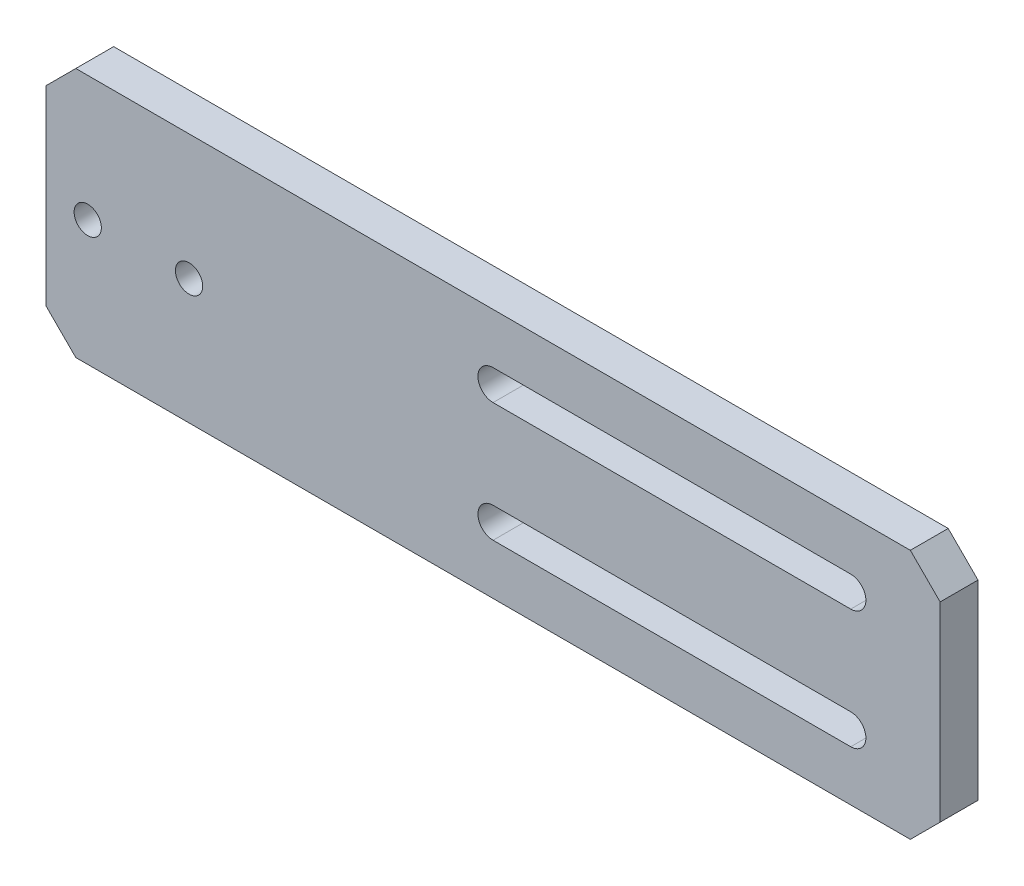
SolidWorks part; units mm, degrees
ref_plane "Front Plane" through (0, 0, 0) normal (0, 0, 1) x (1, 0, 0)
ref_plane "Top Plane" through (0, 0, 0) normal (0, 1, 0) x (1, 0, 0)
ref_plane "Right Plane" through (0, 0, 0) normal (1, 0, 0) x (0, 0, -1)
sketch "Sketch1" plane through (0, 0, 0) normal (0, 0, 1) x (1, 0, 0)
  line L1 (-100, 21) -> (100, 21)
  line L2 (-100, 21) -> (-100, -21)
  line L3 (-100, -21) -> (100, -21)
  line L4 (100, 21) -> (100, -21)
  line L5 (-100, 21) -> (100, -21) construction
  line L6 (-100, -21) -> (100, 21) construction
  point P0 (0, 0)
  dimension "D1" = 200
  dimension "D2" = 42
extrude "Boss-Extrude1" add sketch "Sketch1" along normal blind 6.35
sketch "Sketch3" plane through (0, 0, 6.35) normal (0, 0, 1) x (1, 0, 0)
  line L0 (-60, 10) -> (-60, -10) construction
  line L1 (-100, 21) -> (-100, -21) construction
  circle A0 centre (-60, 10) radius 2
  circle A1 centre (-60, -10) radius 2
  point P4 (-60, 0)
  dimension "D1" = 4
  dimension "D2" = 20
  dimension "D3" = 40
sketch "Sketch4" plane through (0, 0, 6.35) normal (0, 0, 1) x (1, 0, 0)
  line L0 (-100, 21) -> (-100, -21) construction
  line L1 (100, -21) -> (100, 21) construction
  circle A0 centre (-76, 0) radius 2.286
  circle A1 centre (80, 0) radius 2.286 construction
  dimension "D2" = 4.572
  dimension "D3" = 20
  dimension "D1" = 24
  dimension "D4" = 156
extrude "Cut-Extrude3" cut sketch "Sketch4" against normal through all
chamfer "Chamfer1" distance 5 angle 45 4 edges at (-100, 21, 3.175) (-100, -21, 3.175) (100, 21, 3.175) (100, -21, 3.175)
sketch "Sketch5" [suppressed] plane through (0, 0, 6.35) normal (0, 0, 1) x (1, 0, 0)
  line L0 (100, -16) -> (100, 16) construction
  circle A0 centre (77, 0) radius 11
  dimension "D1" = 22
  dimension "D2" = 23
extrude "Cut-Extrude4" [suppressed] cut sketch "Sketch5" against normal blind 25
sketch "Sketch8" plane through (0, 0, 6.35) normal (0, 0, 1) x (1, 0, 0)
  line L4 (25.5, 3.175) -> (10.5, 3.175)
  line L5 (10.5, 3.175) -> (10.5, -3.175)
  line L6 (10.5, -3.175) -> (25.5, -3.175)
  line L7 (25.5, -3.175) -> (25.5, 3.175)
  line L8 (25.5, 3.175) -> (10.5, 3.175)
  line L9 (10.5, 3.175) -> (10.5, -3.175)
  line L10 (10.5, -3.175) -> (25.5, -3.175)
  line L11 (25.5, -3.175) -> (25.5, 3.175)
  dimension "D1" = 0
extrude "Cut-Extrude7" [suppressed] cut sketch "Sketch8" against normal through all
sketch "Sketch9" plane through (0, 0, 6.35) normal (0, 0, 1) x (1, 0, 0)
  circle A0 centre (80, 0) radius 2.286 construction
  circle A1 centre (80, 0) radius 2.286
extrude "Cut-Extrude8" cut sketch "Sketch9" against normal through all
sketch "Sketch10" [suppressed] plane through (0, 0, 6.35) normal (0, 0, 1) x (1, 0, 0)
  circle A0 centre (80, 0) radius 15
  dimension "D1" = 25
extrude "Cut-Extrude9" [suppressed] cut sketch "Sketch10" against normal through all
sketch "Sketch11" plane through (0, 0, 6.35) normal (0, 0, 1) x (1, 0, 0)
  circle A0 centre (95.5563, 15.5563) radius 1.5 construction
  circle A1 centre (64.4437, 15.5563) radius 1.5 construction
  circle A2 centre (95.5563, -15.5563) radius 1.5 construction
  circle A3 centre (64.4437, -15.5563) radius 1.5 construction
  circle A4 centre (95.5563, 15.5563) radius 1.5
  circle A5 centre (64.4437, 15.5563) radius 1.5
  circle A6 centre (95.5563, -15.5563) radius 1.5
  circle A7 centre (64.4437, -15.5563) radius 1.5
sketch "Sketch12" plane through (0, 0, 6.35) normal (0, 0, 1) x (1, 0, 0)
  line L0 (-100, 16) -> (-100, -16) construction
  circle A0 centre (-93, 0) radius 2.286
  point P4 (-100, 0)
  dimension "D1" = 4.572
  dimension "D2" = 7
extrude "Cut-Extrude11" cut sketch "Sketch12" against normal through all
sketch "Sketch13" plane through (0, 0, 6.35) normal (0, 0, 1) x (1, 0, 0)
  line L0 (50, 16) -> (50, -16)
  line L1 (45, 21) -> (50, 16)
  line L2 (50, -16) -> (45, -21)
  line L3 (-95, -21) -> (95, -21) construction
  line L4 (95, 21) -> (-95, 21) construction
  line L5 (-95, -21) -> (95, -21)
  line L6 (95, 21) -> (-95, 21)
  line L7 (-25, 10) -> (35, 10) construction
  line L8 (95, 21) -> (-95, 21)
  line L9 (-95, 21) -> (-100, 16)
  line L10 (-100, 16) -> (-100, -16)
  line L11 (-100, -16) -> (-95, -21)
  line L12 (-95, -21) -> (95, -21)
  line L13 (95, -21) -> (100, -16)
  line L14 (100, -16) -> (100, 16)
  line L15 (100, 16) -> (95, 21)
  line L16 (45, 21) -> (-95, 21)
  line L17 (-95, 21) -> (-100, 16)
  line L18 (-100, 16) -> (-100, -16)
  line L19 (-100, -16) -> (-95, -21)
  line L20 (-95, -21) -> (45, -21)
  line L21 (95, -21) -> (100, -16)
  line L22 (100, -16) -> (100, 16)
  line L23 (100, 16) -> (95, 21)
  line L24 (-25, 12.54) -> (35, 12.54)
  line L25 (-25, 7.46) -> (35, 7.46)
  line L26 (0, 0) -> (50, 0) construction
  line L27 (-25, -10) -> (35, -10) construction
  line L28 (-25, -12.54) -> (35, -12.54)
  line L29 (-25, -7.46) -> (35, -7.46)
  arc A0 (-25, 12.54) -> (-25, 7.46) centre (-25, 10) ccw
  arc A1 (35, 7.46) -> (35, 12.54) centre (35, 10) ccw
  arc A2 (-25, -12.54) -> (-25, -7.46) centre (-25, -10) cw
  arc A3 (35, -7.46) -> (35, -12.54) centre (35, -10) cw
  point P2 (50, 21)
  point P9 (50, -21)
  point P16 (5, 10)
  point P27 (5, -10)
  circle M19 centre (80, 0) radius 2.286
  line M21 (95, 21) -> (-95, 21)
  line M25 (-95, -21) -> (95, -21)
  line M26 (95, -21) -> (100, -16)
  line M27 (100, -16) -> (100, 16)
  line M28 (100, 16) -> (95, 21)
  dimension "D8" = 2.54
  dimension "D2" = 150
  dimension "D3" = 10
  dimension "D4" = 15
  dimension "D7" = 60
  dimension "D1" = 0
extrude "Cut-Extrude12" cut sketch "Sketch13" against normal blind 10 contours L0 L2 L1 M25 M26 M27 M28 M21 M19 | A3 L29 A2 L28 | L25 A1 L24 A0
